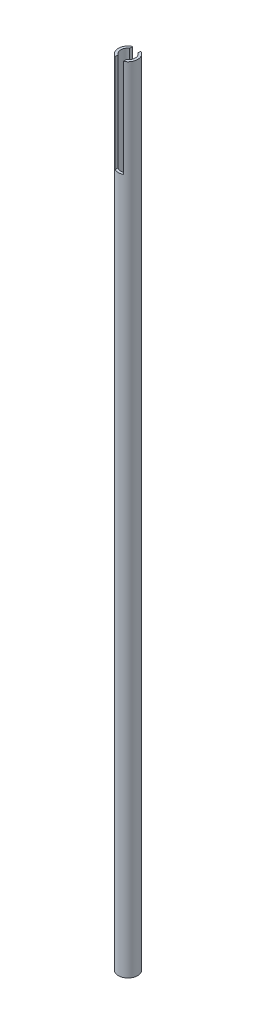
SolidWorks part; units mm, degrees
ref_plane "Front Plane" through (0, 0, 0) normal (0, 0, 1) x (1, 0, 0)
ref_plane "Top Plane" through (0, 0, 0) normal (0, 1, 0) x (1, 0, 0)
ref_plane "Right Plane" through (0, 0, 0) normal (1, 0, 0) x (0, 0, -1)
sketch "Sketch1" plane through (0, 0, 0) normal (0, 1, 0) x (1, 0, 0)
  circle A0 centre (0, 0) radius 10.7125
  circle A1 centre (0, 0) radius 7.9375
  dimension "D1" = 21.4249
  dimension "D2" = 15.875
extrude "Boss-Extrude1" add sketch "Sketch1" along normal blind 879.475
sketch "Sketch2" plane through (0, 879.475, 0) normal (0, 1, 0) x (1, 0, 0)
  line L1 (-4.572, -10.7125) -> (4.572, -10.7125)
  line L2 (-4.572, -10.7125) -> (-4.572, 10.7125)
  line L3 (-4.572, 10.7125) -> (4.572, 10.7125)
  line L4 (4.572, -10.7125) -> (4.572, 10.7125)
  line L5 (-4.572, -10.7125) -> (4.572, 10.7125) construction
  line L6 (-4.572, 10.7125) -> (4.572, -10.7125) construction
  circle A0 centre (0, 0) radius 10.7125 construction
  point P0 (0, 0)
extrude "Cut-Extrude1" cut sketch "Sketch2" against normal blind 108.585
